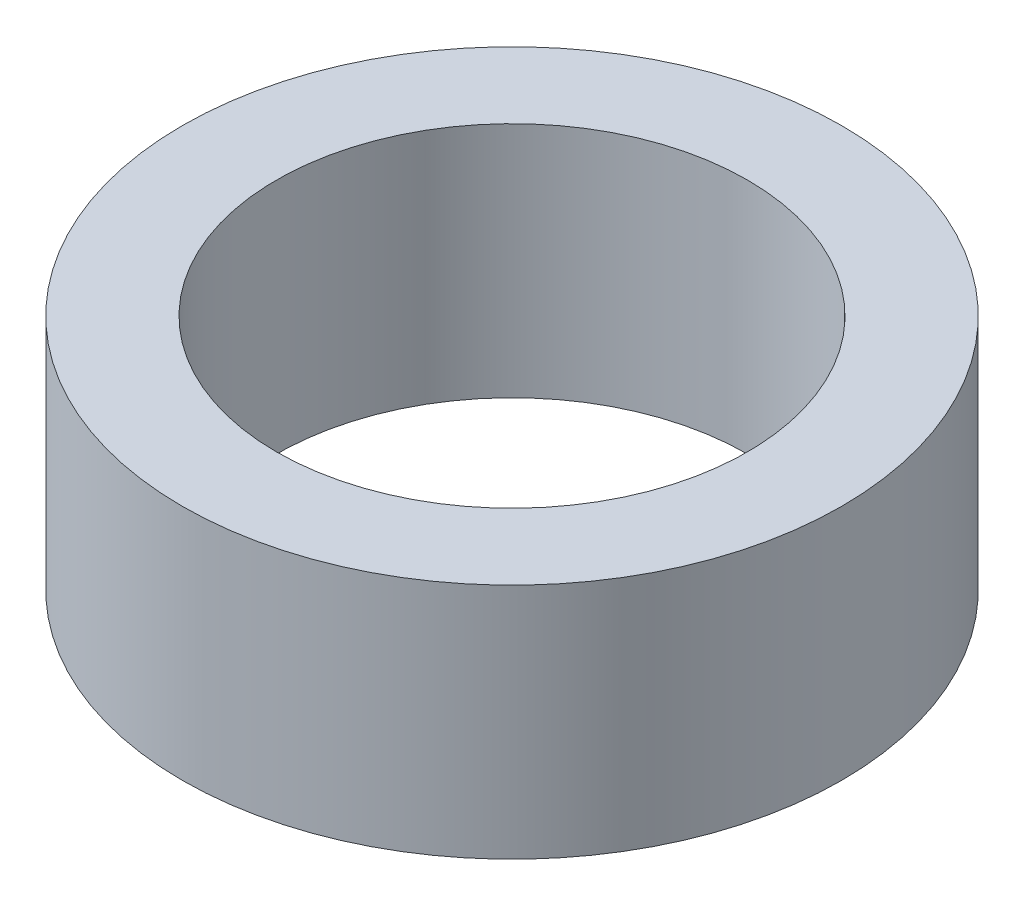
SolidWorks part; units mm, degrees
ref_plane "前视基准面" through (0, 0, 0) normal (0, 0, 1) x (1, 0, 0)
ref_plane "上视基准面" through (0, 0, 0) normal (0, 1, 0) x (1, 0, 0)
ref_plane "右视基准面" through (0, 0, 0) normal (1, 0, 0) x (0, 0, -1)
sketch "草图1" plane through (0, 0, 0) normal (0, 1, 0) x (1, 0, 0)
  circle A0 centre (0, 0) radius 1.5875
  circle A1 centre (0, 0) radius 2.2225
  dimension "D1" = 3.175
  dimension "D2" = 4.445
extrude "凸台-拉伸1" add sketch "草图1" along normal blind 1.6
